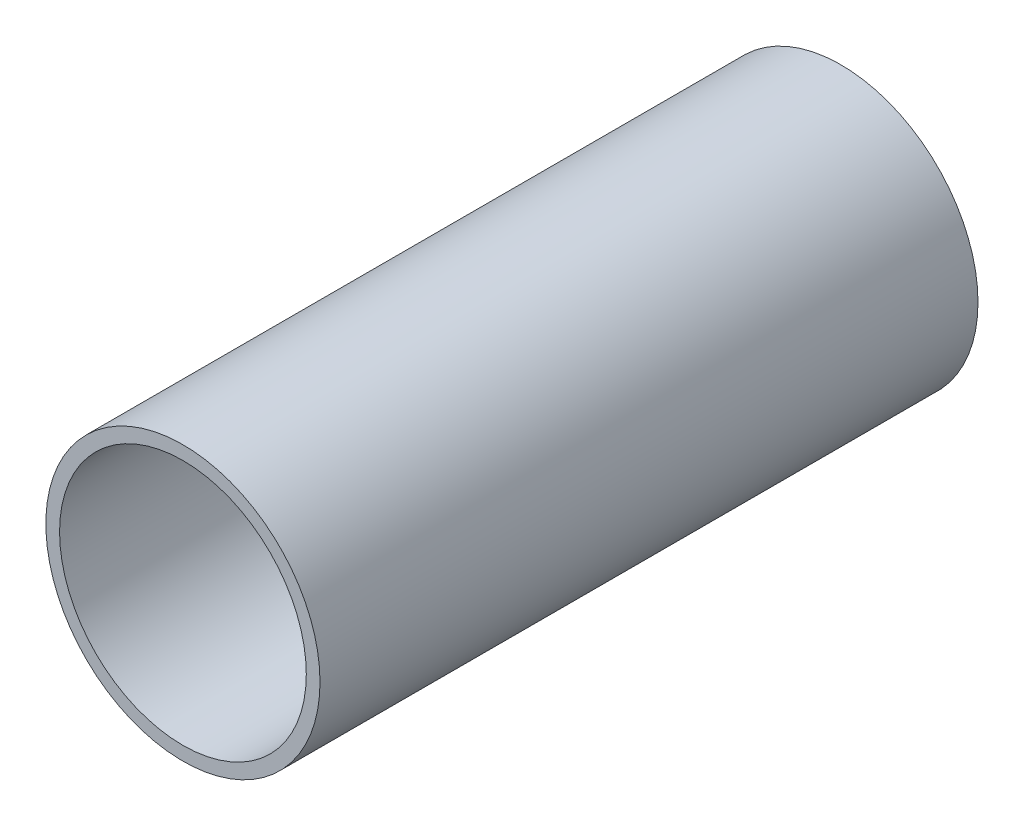
SolidWorks part; units mm, degrees
material "6061 Alloy"
ref_plane "Front Plane" through (0, 0, 0) normal (0, 0, 1) x (1, 0, 0)
ref_plane "Top Plane" through (0, 0, 0) normal (0, 1, 0) x (1, 0, 0)
ref_plane "Right Plane" through (0, 0, 0) normal (1, 0, 0) x (0, 0, -1)
sketch "Sketch5" plane through (0, 0, 0) normal (0, 0, 1) x (1, 0, 0)
  circle A0 centre (0, 0) radius 28.575
  circle A1 centre (0, 0) radius 31.75
extrude "Boss-Extrude1" add sketch "Sketch5" along normal blind 152.4
